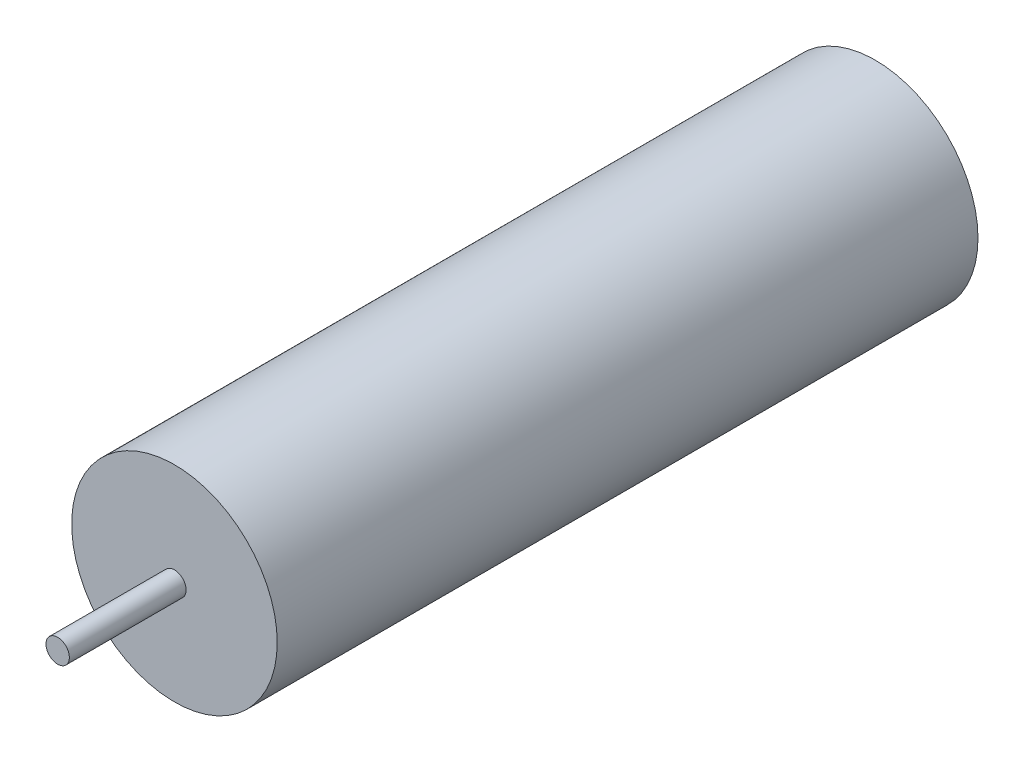
SolidWorks part; units mm, degrees
material "1023 Carbon Steel Sheet (SS)"
ref_plane "Front Plane" through (0, 0, 0) normal (0, 0, 1) x (1, 0, 0)
ref_plane "Top Plane" through (0, 0, 0) normal (0, 1, 0) x (1, 0, 0)
ref_plane "Right Plane" through (0, 0, 0) normal (1, 0, 0) x (0, 0, -1)
sketch "Sketch1" plane through (0, 0, 0) normal (0, 0, 1) x (1, 0, 0)
  circle A0 centre (0, -25.4) radius 11.176
  circle A1 centre (0, -25.4) radius 11.176 construction
extrude "Boss-Extrude1" add sketch "Sketch1" against normal blind 76.2
sketch "Sketch2" plane through (0, 0, 0) normal (0, 0, 1) x (1, 0, 0)
  circle A0 centre (0, -25.4) radius 1.27
  dimension "D1" = 2.54
extrude "Boss-Extrude2" add sketch "Sketch2" along normal blind 12.7
